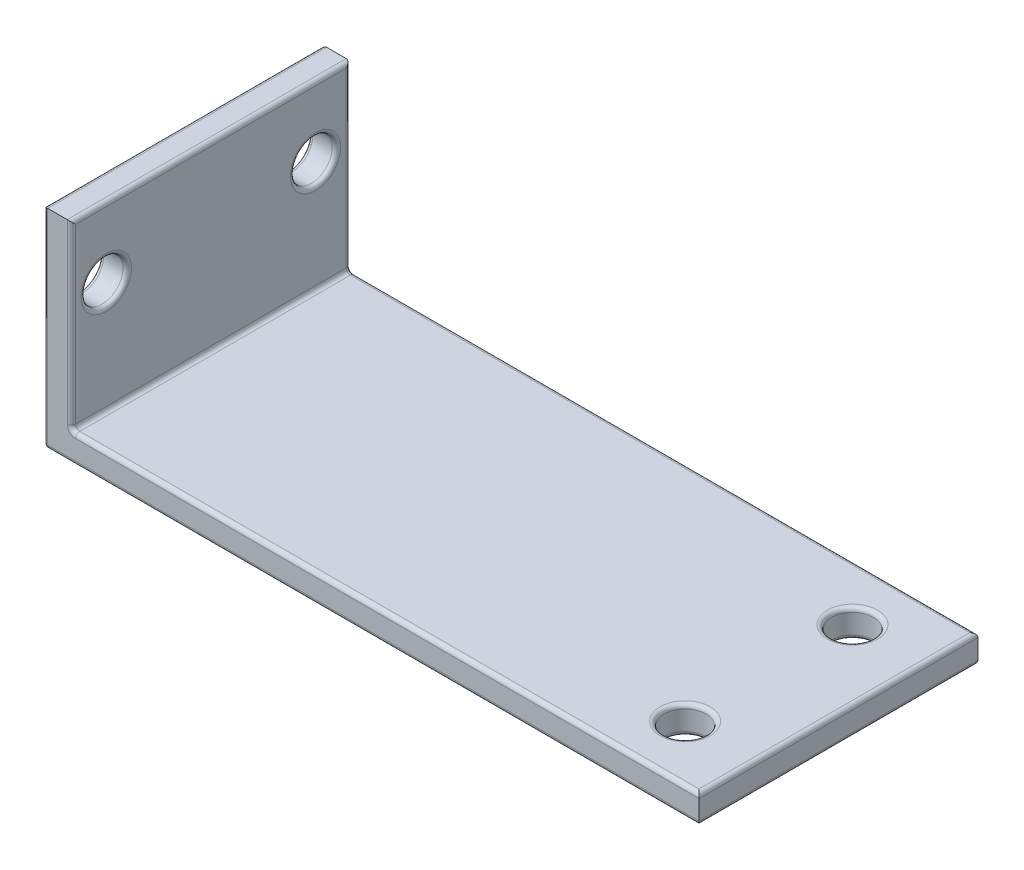
SolidWorks part; units mm, degrees
ref_plane "Front Plane" through (0, 0, 0) normal (0, 0, 1) x (1, 0, 0)
ref_plane "Top Plane" through (0, 0, 0) normal (0, 1, 0) x (1, 0, 0)
ref_plane "Right Plane" through (0, 0, 0) normal (1, 0, 0) x (0, 0, -1)
sketch "Sketch1" plane through (0, 0, 0) normal (0, 0, 1) x (1, 0, 0)
  line L0 (-625.3715, 0) -> (30643.2047, 0) construction
  line L1 (0, -625.3715) -> (0, 30643.2047) construction
  line L2 (0, 0) -> (47, 0)
  line L3 (47, 0) -> (47, 2)
  line L4 (47, 2) -> (2, 2)
  line L5 (2, 2) -> (2, 15)
  line L6 (2, 15) -> (0, 15)
  line L7 (0, 15) -> (0, 0)
  dimension "D1" = 47
  dimension "D2" = 2
  dimension "D3" = 2
  dimension "D4" = 15
extrude "Boss-Extrude1" add sketch "Sketch1" along normal mid plane 20
sketch "Sketch2" plane through (0, 0, 0) normal (-1, 0, 0) x (0, 0, 1)
  line L0 (0, -1000) -> (0, 49000) construction
  line L1 (10, 15) -> (-10, 15) construction
  circle A1 centre (7.5, 10) radius 1.5
  circle A2 centre (-7.5, 10) radius 1.5
  dimension "D1" = 3
  dimension "D2" = 7.5
  dimension "D3" = 5
extrude "Cut-Extrude1" cut sketch "Sketch2" against normal through all
sketch "Sketch3" plane through (0, 0, 0) normal (0, -1, 0) x (1, 0, 0)
  line L0 (-1000, 0) -> (49000, 0) construction
  line L1 (47, 10) -> (47, -10) construction
  circle A0 centre (42, 6) radius 1.5
  circle A1 centre (42, -6) radius 1.5
  dimension "D1" = 3
  dimension "D2" = 6
  dimension "D3" = 5
extrude "Cut-Extrude2" cut sketch "Sketch3" against normal through all
fillet "Fillet1" radius 0.3 22 edges at (2, 8.5, 10) (2, 15, 0) (2, 8.5, -10) (2, 8.5, -7.5) (2, 8.5, 7.5) (47, 2, 0) (24.5, 2, 10) (2, 2, 0) (24.5, 2, -10) (43.5, 2, -6) (43.5, 2, 6) (23.5, 0, 10) (47, 0, 0) (23.5, 0, -10) (42, 0, -4.5) (42, 0, 4.5) (0, 15, 0) (0, 7.5, 10) (0, 0, 0) (0, 7.5, -10) (0, 10, -9) (0, 10, 9)
